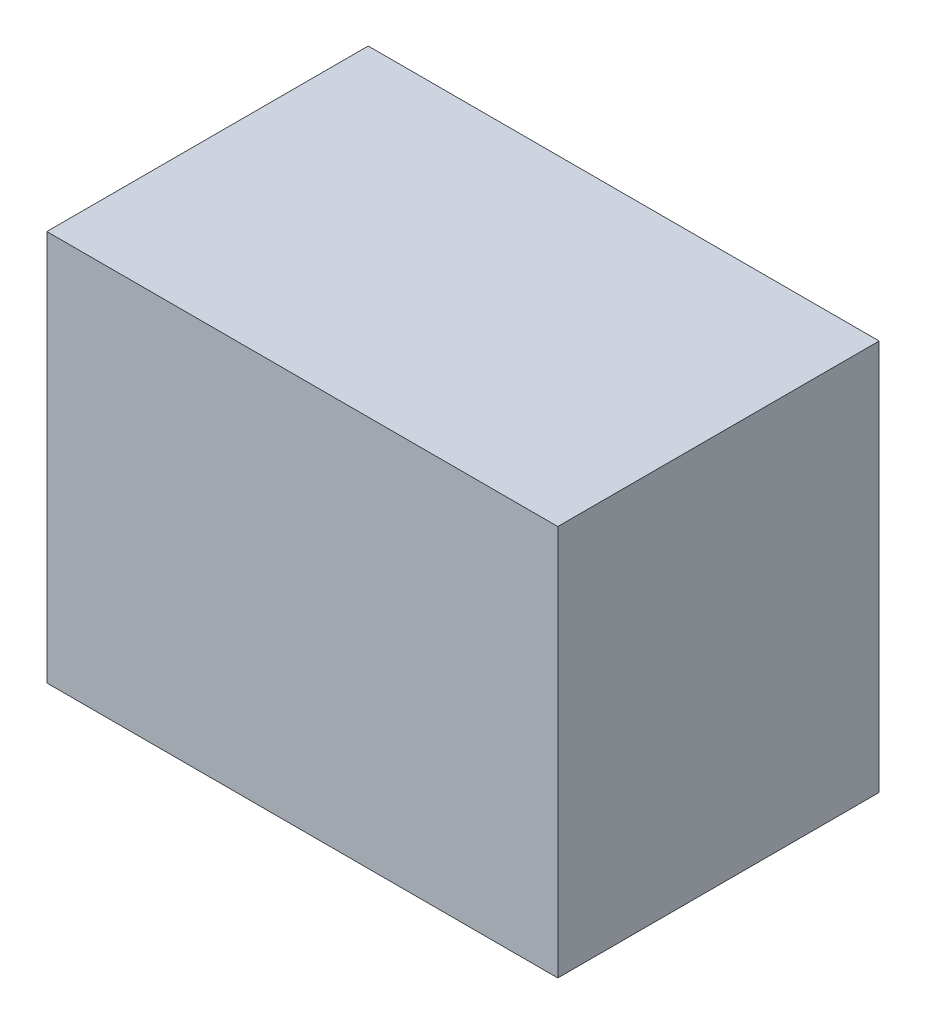
SolidWorks part; units mm, degrees
ref_plane "Front Plane" through (0, 0, 0) normal (0, 0, 1) x (1, 0, 0)
ref_plane "Top Plane" through (0, 0, 0) normal (0, 1, 0) x (1, 0, 0)
ref_plane "Right Plane" through (0, 0, 0) normal (1, 0, 0) x (0, 0, -1)
sketch "PowerThing Sketch" plane through (0, 0, 0) normal (0, 1, 0) x (1, 0, 0)
  line L1 (0, 0) -> (14.31, 0)
  line L2 (0, 0) -> (0, 9)
  line L3 (0, 9) -> (14.31, 9)
  line L4 (14.31, 0) -> (14.31, 9)
  dimension "PowerThingWidth" = 14.31
  dimension "PowerThingLength" = 9
extrude "PowerThing Extrude" add sketch "PowerThing Sketch" along normal blind 10.95
